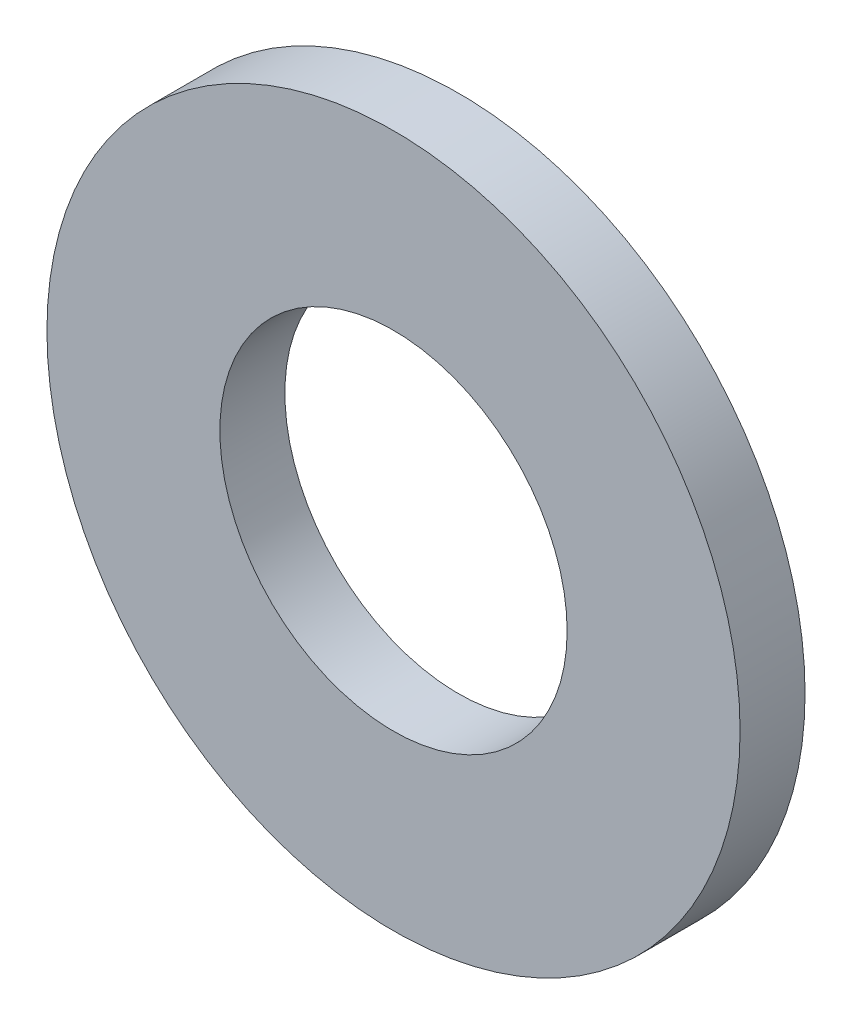
SolidWorks part; units mm, degrees
material "Leaded Commercial Bronze"
ref_plane "Front Plane" through (0, 0, 0) normal (0, 0, 1) x (1, 0, 0)
ref_plane "Top Plane" through (0, 0, 0) normal (0, 1, 0) x (1, 0, 0)
ref_plane "Right Plane" through (0, 0, 0) normal (1, 0, 0) x (0, 0, -1)
sketch "Sketch1" plane through (0, 0, 0) normal (0, 0, 1) x (1, 0, 0)
  circle A0 centre (0, 0) radius 12.7
  circle A1 centre (0, 0) radius 6.3627
  dimension "D1" = 25.4
  dimension "ID" = 12.7254
extrude "Extrude1" add sketch "Sketch1" along normal mid plane 2.3813
sketch "Sketch2" plane through (0, 0, 0) normal (1, 0, 0) x (0, 0, -1)
  line L0 (-1.1906, -6.3627) -> (1.1906, -6.3627) construction
  line L3 (1.1906, 6.3627) -> (-1.1906, 6.3627) construction
  line L5 (-1.1906, -6.3627) -> (1.1906, -6.3627)
  line L6 (1.1906, 6.3627) -> (-1.1906, 6.3627)
sketch "Sketch4" plane through (0, 0, 1.1906) normal (0, 0, 1) x (1, 0, 0)
  line L0 (0, 0) -> (-4.4991, 4.4991)
  line L1 (0, -1.7463) -> (0, 1.7463) construction
  circle A0 centre (0, 0) radius 6.3627 construction
  dimension "D1" = 45
